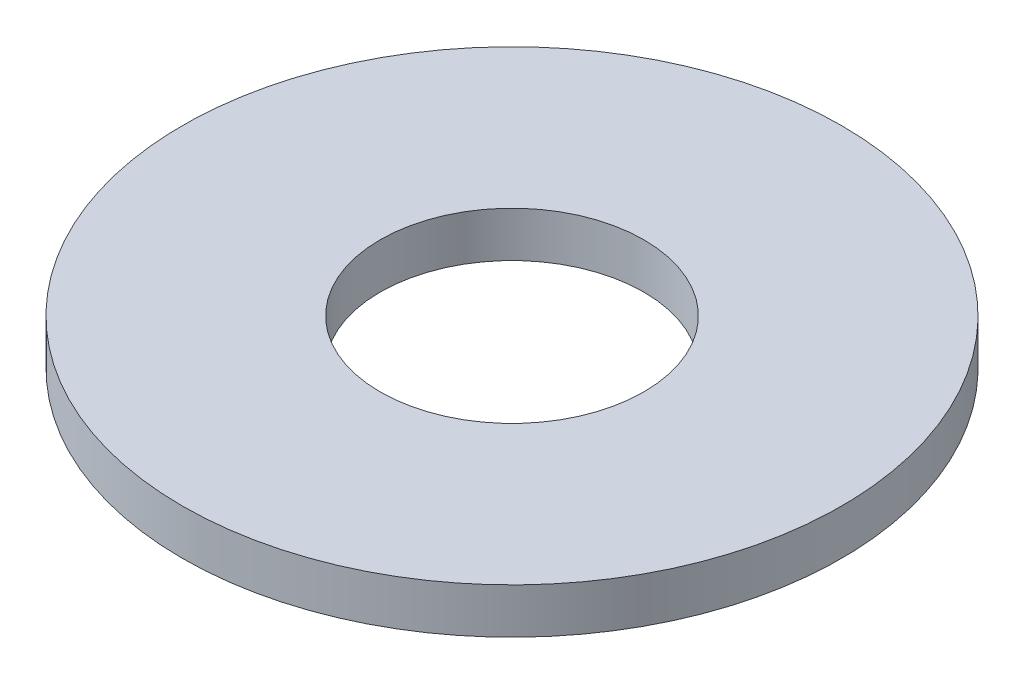
SolidWorks part; units mm, degrees
ref_plane "Front Plane" through (0, 0, 0) normal (0, 0, 1) x (1, 0, 0)
ref_plane "Top Plane" through (0, 0, 0) normal (0, 1, 0) x (1, 0, 0)
ref_plane "Right Plane" through (0, 0, 0) normal (1, 0, 0) x (0, 0, -1)
sketch "Sketch1" plane through (0, 0, 0) normal (0, 1, 0) x (1, 0, 0)
  circle A0 centre (0, 0) radius 7.9375
  dimension "OD" = 15.875
extrude "Boss-Extrude1" add sketch "Sketch1" along normal blind 1.0922
sketch "Sketch5" plane through (0, 1.0922, 0) normal (0, 1, 0) x (-1, 0, 0)
  circle A0 centre (0, 0) radius 3.175
  dimension "ID" = 6.35
extrude "Cut-Extrude1" cut sketch "Sketch5" against normal through all
